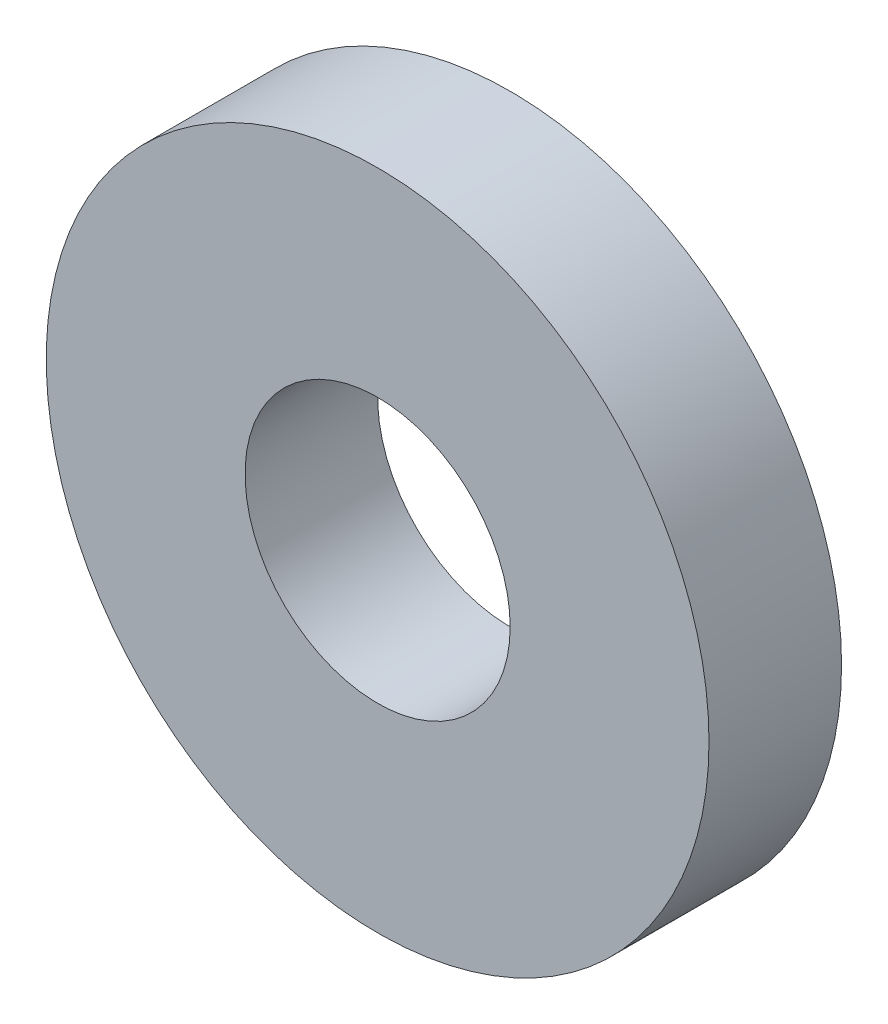
SolidWorks part; units mm, degrees
ref_plane "Front Plane" through (0, 0, 0) normal (0, 0, 1) x (1, 0, 0)
ref_plane "Top Plane" through (0, 0, 0) normal (0, 1, 0) x (1, 0, 0)
ref_plane "Right Plane" through (0, 0, 0) normal (1, 0, 0) x (0, 0, -1)
sketch "Sketch1" plane through (0, 0, 0) normal (0, 0, 1) x (1, 0, 0)
  circle A0 centre (0, 92.5) radius 12.5
  arc A1 (28.6182, 41) -> (-28.6182, 41) centre (0, 50) ccw construction
  circle A2 centre (0, 92.5) radius 5
  dimension "D1" = 25
  dimension "D2" = 10
extrude "Boss-Extrude1" add sketch "Sketch1" along normal blind 5
